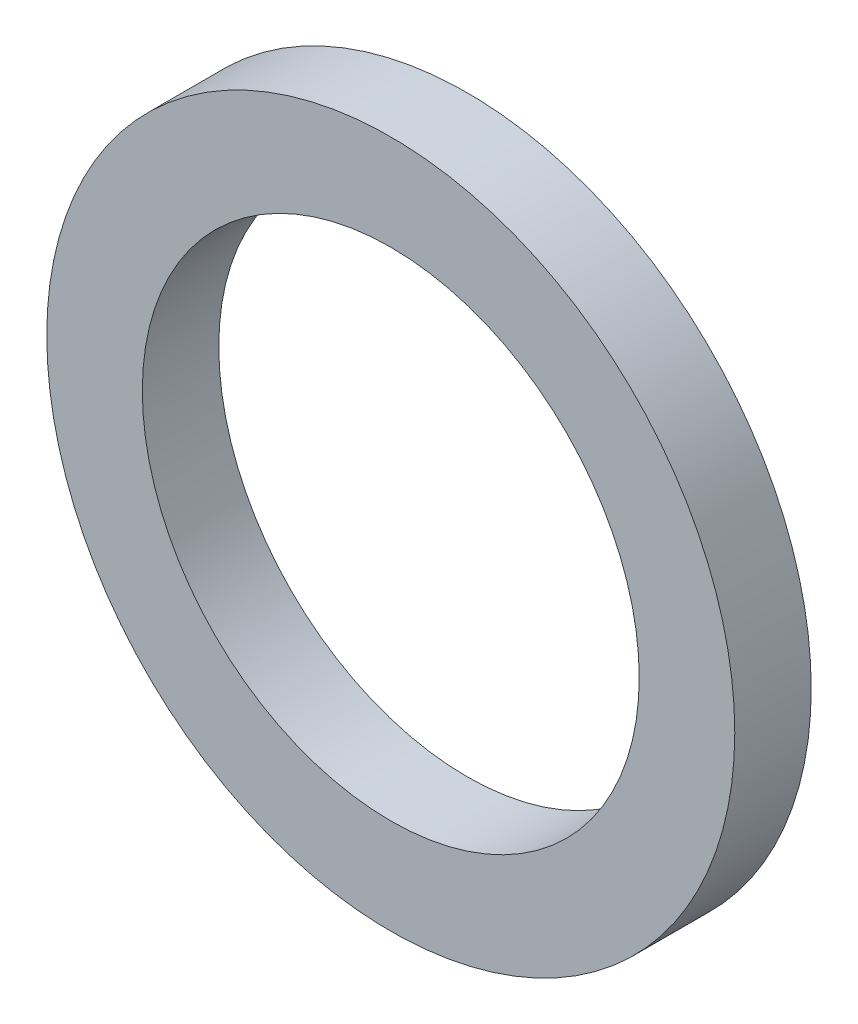
SolidWorks part; units mm, degrees
ref_plane "前视基准面" through (0, 0, 0) normal (0, 0, 1) x (1, 0, 0)
ref_plane "上视基准面" through (0, 0, 0) normal (0, 1, 0) x (1, 0, 0)
ref_plane "右视基准面" through (0, 0, 0) normal (1, 0, 0) x (0, 0, -1)
sketch "草图1" plane through (0, 0, 0) normal (0, 0, 1) x (1, 0, 0)
  circle A0 centre (0, 0) radius 3.9
  circle A1 centre (0, 0) radius 5.4
extrude "凸台-拉伸1" add sketch "草图1" along normal blind 1.2
